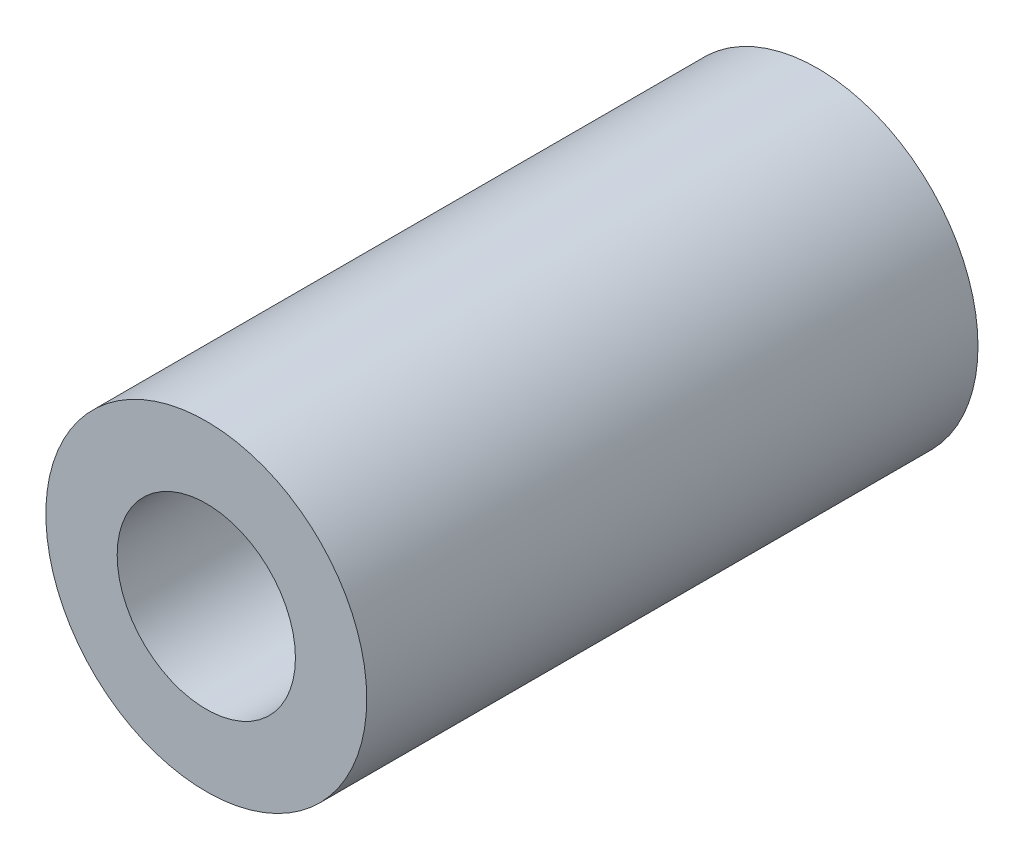
SolidWorks part; units mm, degrees
material "PBT Uniwersalny"
ref_plane "Płaszczyzna przednia" through (0, 0, 0) normal (0, 0, 1) x (1, 0, 0)
ref_plane "Płaszczyzna górna" through (0, 0, 0) normal (0, 1, 0) x (1, 0, 0)
ref_plane "Płaszczyzna prawa" through (0, 0, 0) normal (1, 0, 0) x (0, 0, -1)
sketch "Szkic1" plane through (0, 0, 0) normal (0, 0, 1) x (1, 0, 0)
  circle A1 centre (0, 0) radius 1.75
  circle A2 centre (0, 0) radius 3.15
  dimension "D2" = 3.5
  dimension "D1" = 6.3
extrude "Dodanie-wyciągnięcie1" add sketch "Szkic1" along normal blind 12
